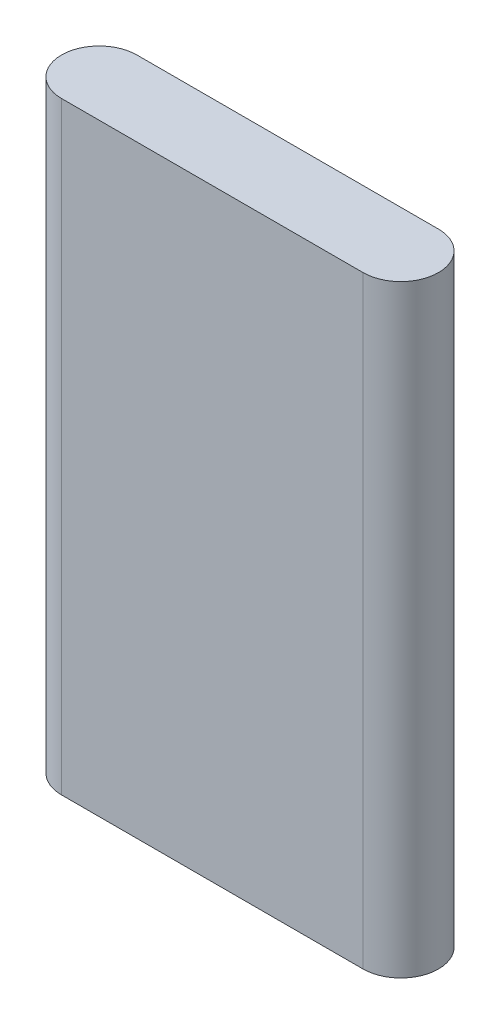
SolidWorks part; units mm, degrees
ref_plane "Ön Düzlem" through (0, 0, 0) normal (0, 0, 1) x (1, 0, 0)
ref_plane "Üst Düzlem" through (0, 0, 0) normal (0, 1, 0) x (1, 0, 0)
ref_plane "Sağ Düzlem" through (0, 0, 0) normal (1, 0, 0) x (0, 0, -1)
sketch "Çizim2" plane through (0, 0, 0) normal (0, 1, 0) x (1, 0, 0)
  line L0 (-20.3145, 0) -> (19.6855, 0) construction
  line L1 (-20.3145, 5) -> (19.6855, 5)
  line L2 (-20.3145, -5) -> (19.6855, -5)
  line L3 (-25.3145, 0) -> (-25.3145, 16.6935) construction
  line L4 (24.6855, 0) -> (24.6855, 18.9268) construction
  arc A0 (-20.3145, 5) -> (-20.3145, -5) centre (-20.3145, 0) ccw
  arc A1 (19.6855, -5) -> (19.6855, 5) centre (19.6855, 0) ccw
  point P3 (-0.3145, 0)
  dimension "D2" = 50
  dimension "D1" = 10
extrude "Yükseklik-Ekstrüzyon1" add sketch "Çizim2" along normal blind 80
